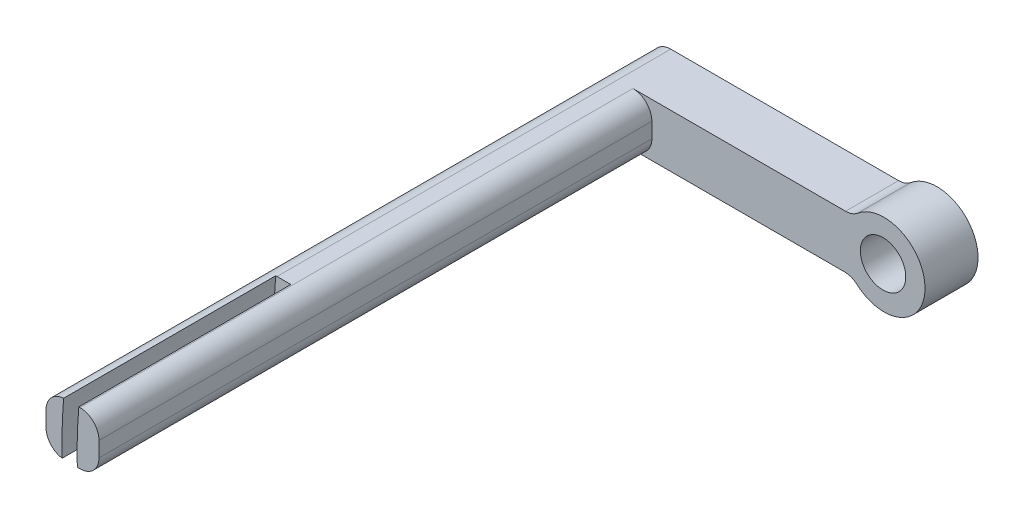
SolidWorks part; units mm, degrees
ref_plane "Front Plane" through (0, 0, 0) normal (0, 0, 1) x (1, 0, 0)
ref_plane "Top Plane" through (0, 0, 0) normal (0, 1, 0) x (1, 0, 0)
ref_plane "Right Plane" through (0, 0, 0) normal (1, 0, 0) x (0, 0, -1)
sketch "Sketch1" plane through (0, 0, 0) normal (0, 1, 0) x (1, 0, 0)
  line L1 (-6.2973, 55.1954) -> (0.7027, 55.1954)
  line L2 (-6.2973, 55.1954) -> (-6.2973, -24.8046)
  line L3 (-6.2973, -24.8046) -> (0.7027, -24.8046)
  line L4 (0.7027, 48.1954) -> (0.7027, -24.8046)
  line L5 (-6.2973, 55.1954) -> (0.7027, -24.8046) construction
  line L6 (-6.2973, -24.8046) -> (-2.7973, 15.1954) construction
  line L7 (0.7027, 55.1954) -> (33.7027, 55.1954)
  line L9 (0.7027, 48.1954) -> (33.7027, 48.1954)
  line L10 (33.7027, 55.1954) -> (33.7027, 48.1954)
  point P0 (-2.7973, 15.1954)
  point P9 (0, 0)
  point P10 (0, 0)
  dimension "D1" = 80
  dimension "D2" = 7
  dimension "D3" = 7
  dimension "D4" = 33
extrude "Boss-Extrude1" add sketch "Sketch1" along normal blind 7
fillet "Fillet1" radius 2.5 4 edges at (0.7027, 0, -11.6954) (0.7027, 7, -11.6954) (-6.2973, 7, -15.1954) (-6.2973, 0, -15.1954)
sketch "Sketch2" plane through (0, 0, -55.1954) normal (0, 0, -1) x (-1, 0, 0)
  circle A0 centre (-31.3628, 3.4352) radius 5.4105
  point P2 (-31.3628, 3.4352)
extrude "Boss-Extrude2" add sketch "Sketch2" against normal blind 7
fillet "Fillet2" radius 2.5 2 edges at (27.1826, 0, -51.6954) (27.2926, 7, -51.6954)
sketch "Sketch3" plane through (0, 0, -55.1954) normal (0, 0, -1) x (-1, 0, 0)
  circle A0 centre (-31.2299, 3.4605) radius 3
  point P2 (-31.2299, 3.4605)
  dimension "D1" = 6
extrude "Cut-Extrude1" cut sketch "Sketch3" against normal blind 16
sketch "Sketch4" plane through (0, 0, 24.8046) normal (0, 0, 1) x (1, 0, 0)
  circle A0 centre (58.8086, 1.743) radius 61
  circle A1 centre (58.8086, 1.743) radius 63
  point P2 (58.8086, 1.743)
  dimension "D1" = 122
  dimension "D2" = 2
extrude "Cut-Extrude2" cut sketch "Sketch4" against normal blind 28
